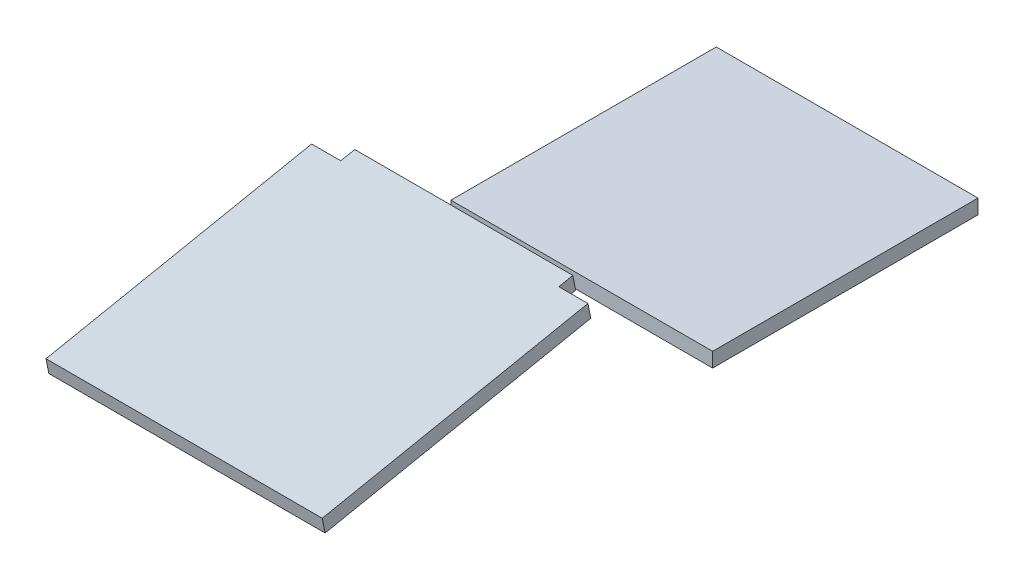
SolidWorks part; units mm, degrees
ref_plane "Front Plane" through (0, 0, 0) normal (0, 0, 1) x (1, 0, 0)
ref_plane "Top Plane" through (0, 0, 0) normal (0, 1, 0) x (1, 0, 0)
ref_plane "Right Plane" through (0, 0, 0) normal (1, 0, 0) x (0, 0, -1)
sketch "Sketch1" plane through (0, 0, 0) normal (0, 1, 0) x (1, 0, 0)
  line L1 (-228.6, 231.775) -> (228.6, 231.775)
  line L2 (-228.6, 231.775) -> (-228.6, -231.775)
  line L3 (-228.6, -231.775) -> (228.6, -231.775)
  line L4 (228.6, 231.775) -> (228.6, -231.775)
  line L5 (-228.6, 231.775) -> (228.6, -231.775) construction
  line L6 (-228.6, -231.775) -> (228.6, 231.775) construction
  line L7 (-190.5, -384.175) -> (190.5, -384.175)
  line L8 (-190.5, -384.175) -> (-190.5, -892.175)
  line L9 (-190.5, -892.175) -> (190.5, -892.175)
  line L10 (190.5, -384.175) -> (190.5, -892.175)
  line L11 (-190.5, -384.175) -> (190.5, -892.175) construction
  line L12 (-190.5, -892.175) -> (190.5, -384.175) construction
  line L13 (190.5, -409.575) -> (241.3, -409.575)
  line L14 (190.5, -409.575) -> (190.5, -892.175)
  line L15 (190.5, -892.175) -> (241.3, -892.175)
  line L16 (241.3, -409.575) -> (241.3, -892.175)
  line L17 (-190.5, -409.575) -> (-241.3, -409.575)
  line L18 (-190.5, -409.575) -> (-190.5, -892.175)
  line L19 (-190.5, -892.175) -> (-241.3, -892.175)
  line L20 (-241.3, -409.575) -> (-241.3, -892.175)
  point P0 (0, 0)
  point P6 (0, -638.175)
  dimension "D1" = 463.55
  dimension "D2" = 457.2
  dimension "D3" = 660.4
  dimension "D4" = 381
  dimension "D5" = 508
  dimension "D6" = 50.8
  dimension "D7" = 50.8
  dimension "D8" = 25.4
  dimension "D9" = 25.4
sketch "Sketch2" plane through (0, 0, 0) normal (1, 0, 0) x (0, 0, -1)
  line L0 (-892.175, 177.8) -> (-384.175, 279.4)
  line L1 (-231.775, 69.85) -> (231.775, 69.85)
  line L2 (-384.175, 0) -> (-892.175, 0) construction
  line L3 (-384.175, 0) -> (-892.175, 0) construction
  line L4 (-231.775, 0) -> (231.775, 0) construction
  line L5 (-231.775, 0) -> (231.775, 0) construction
  dimension "D1" = 177.8
  dimension "D2" = 279.4
  dimension "D3" = 69.85
ref_plane "Plane1" through (0, 69.85, 0) normal (0, 1, 0) x (1, 0, 0)
sketch "Sketch3" plane through (0, 69.85, 0) normal (0, 1, 0) x (1, 0, 0)
  line L0 (-228.6, -231.775) -> (228.6, -231.775) construction
  line L1 (-228.6, 231.775) -> (-228.6, -231.775) construction
  line L2 (-228.6, 231.775) -> (228.6, 231.775) construction
  line L3 (228.6, 231.775) -> (228.6, -231.775) construction
  line L4 (-228.6, -231.775) -> (228.6, -231.775)
  line L5 (-228.6, 231.775) -> (-228.6, -231.775)
  line L6 (-228.6, 231.775) -> (228.6, 231.775)
  line L7 (228.6, 231.775) -> (228.6, -231.775)
extrude "Boss-Extrude1" add sketch "Sketch3" against normal blind 25.4
ref_plane "Plane2" through (0, 342.5337, 68.5067) normal (0, -0.9806, -0.1961) x (0, 0.1961, -0.9806)
sketch "Sketch4" plane through (0, 342.5337, 68.5067) normal (0, -0.9806, -0.1961) x (0, 0.1961, -0.9806)
  line L0 (-874.8496, 190.5) -> (-874.8496, 241.3) construction
  line L1 (-874.8496, -190.5) -> (-874.8496, -241.3) construction
  line L2 (-874.8496, -190.5) -> (-874.8496, 190.5) construction
  line L3 (-401.6213, -241.3) -> (-874.8496, -241.3) construction
  line L4 (-401.6213, -190.5) -> (-401.6213, -241.3) construction
  line L5 (-376.7146, -190.5) -> (-874.8496, -190.5) construction
  line L6 (-376.7146, -190.5) -> (-376.7146, 190.5) construction
  line L7 (-401.6213, 190.5) -> (-401.6213, 241.3) construction
  line L8 (-376.7146, 190.5) -> (-874.8496, 190.5) construction
  line L9 (-401.6213, 241.3) -> (-874.8496, 241.3) construction
  line L10 (-874.8496, 190.5) -> (-874.8496, 241.3)
  line L11 (-874.8496, -190.5) -> (-874.8496, -241.3)
  line L12 (-874.8496, -190.5) -> (-874.8496, 190.5)
  line L13 (-401.6213, -241.3) -> (-874.8496, -241.3)
  line L14 (-401.6213, -190.5) -> (-401.6213, -241.3)
  line L15 (-376.7146, -190.5) -> (-401.6213, -190.5)
  line L16 (-376.7146, -190.5) -> (-376.7146, 190.5)
  line L17 (-401.6213, 190.5) -> (-401.6213, 241.3)
  line L18 (-376.7146, 190.5) -> (-401.6213, 190.5)
  line L19 (-401.6213, 241.3) -> (-874.8496, 241.3)
extrude "Boss-Extrude2" add sketch "Sketch4" along normal blind 25.4 separate body
